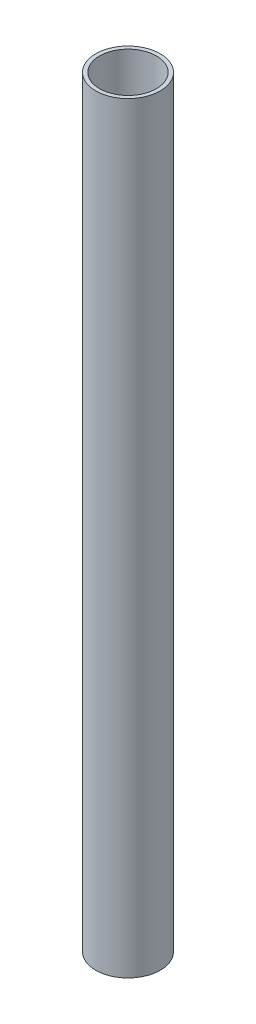
SolidWorks part; units mm, degrees
material "PVC Rigid"
ref_plane "Front Plane" through (0, 0, 0) normal (0, 0, 1) x (1, 0, 0)
ref_plane "Top Plane" through (0, 0, 0) normal (0, 1, 0) x (1, 0, 0)
ref_plane "Right Plane" through (0, 0, 0) normal (1, 0, 0) x (0, 0, -1)
sketch "Sketch1" plane through (0, 0, 0) normal (0, 1, 0) x (1, 0, 0)
  circle A0 centre (0, 0) radius 42.3
extrude "Boss-Extrude1" add sketch "Sketch1" along normal blind 1000
shell "Shell1" thickness 5
